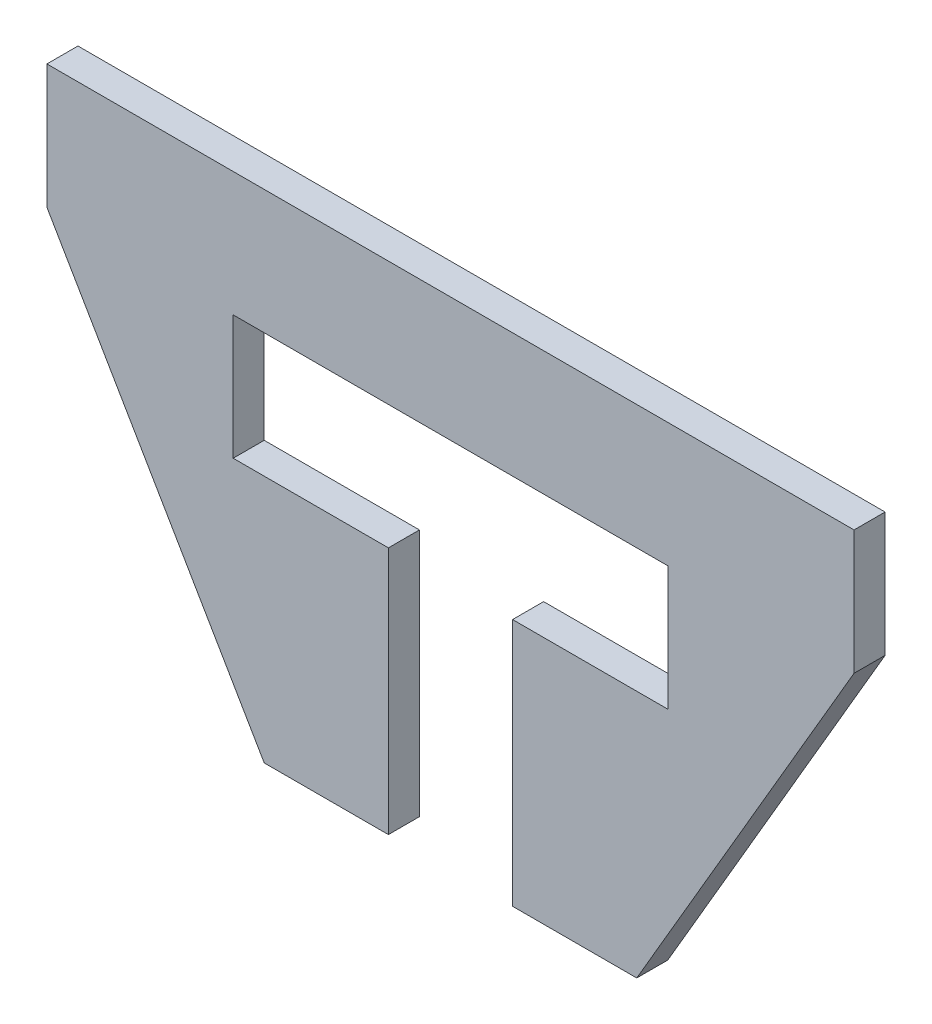
SolidWorks part; units mm, degrees
ref_plane "Front Plane" through (0, 0, 0) normal (0, 0, 1) x (1, 0, 0)
ref_plane "Top Plane" through (0, 0, 0) normal (0, 1, 0) x (1, 0, 0)
ref_plane "Right Plane" through (0, 0, 0) normal (1, 0, 0) x (0, 0, -1)
sketch "Sketch1" plane through (0, 0, 0) normal (0, 0, 1) x (1, 0, 0)
  line L0 (0, 0) -> (165.1, 0)
  line L1 (165.1, 0) -> (165.1, -25.4)
  line L2 (165.1, -25.4) -> (120.65, -101.6)
  line L3 (120.65, -101.6) -> (95.25, -101.6)
  line L4 (95.25, -101.6) -> (95.25, -50.8)
  line L5 (95.25, -50.8) -> (127, -50.8)
  line L6 (127, -50.8) -> (127, -25.4)
  line L7 (127, -25.4) -> (38.1, -25.4)
  line L8 (38.1, -25.4) -> (38.1, -50.8)
  line L9 (38.1, -50.8) -> (69.85, -50.8)
  line L10 (69.85, -50.8) -> (69.85, -101.6)
  line L11 (69.85, -101.6) -> (44.45, -101.6)
  line L12 (44.45, -101.6) -> (0, -25.4)
  line L13 (0, -25.4) -> (0, 0)
  point P3 (0, 0)
  point P16 (0, 0)
  point P17 (0, 0)
  point P18 (120.65, -122.4768)
  point P19 (226.2142, -75.1797)
  point P20 (26.6435, -65.0858)
  point P21 (8.7222, -97.3439)
  point P22 (5.4095, -85.0673)
  point P23 (21.7248, -79.5502)
  point P24 (95.1426, -106.4411)
  point P25 (114.6896, -85.5143)
  point P26 (34.3127, -101.6)
  point P27 (34.7653, -79.2852)
  point P28 (0, 0)
  point P29 (0, 0)
  point P30 (121.6675, -15.4664)
  point P31 (0, 0)
  point P32 (0, 0)
  point P33 (0, 0)
  point P34 (0, 0)
  dimension "D1" = 165.1
  dimension "D2" = 25.4
  dimension "D3" = 101.6
  dimension "D4" = 120.65
  dimension "D5" = 69.85
  dimension "D6" = 44.45
  dimension "D7" = 25.4
  dimension "D8" = 88.9
  dimension "D9" = 25.4
  dimension "D10" = 38.1
extrude "Boss-Extrude1" add sketch "Sketch1" along normal blind 6.35 contours L0 L1 L2 L3 L4 L5 L6 L7 L8 L9 L10 L11 L12 L13
